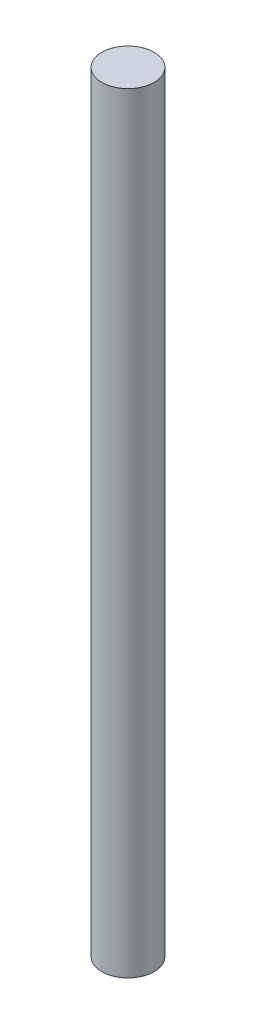
SolidWorks part; units mm, degrees
ref_plane "前视基准面" through (0, 0, 0) normal (0, 0, 1) x (1, 0, 0)
ref_plane "上视基准面" through (0, 0, 0) normal (0, 1, 0) x (1, 0, 0)
ref_plane "右视基准面" through (0, 0, 0) normal (1, 0, 0) x (0, 0, -1)
other "Configuration Table"
sketch "草图1" plane through (0, 0, 0) normal (0, 1, 0) x (1, 0, 0)
  circle A0 centre (0, 0) radius 2
  dimension "D1" = 4
extrude "凸台-拉伸1" add sketch "草图1" along normal blind 59
